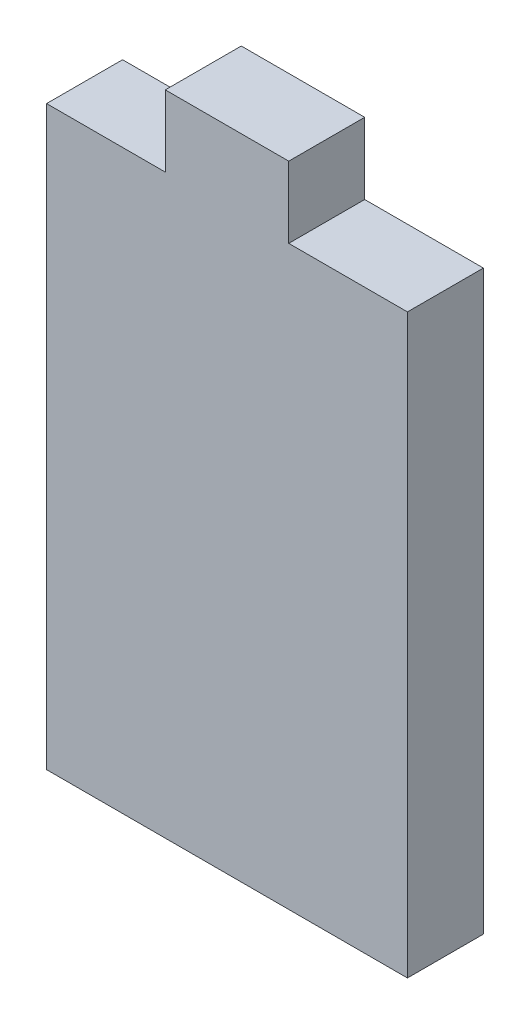
SolidWorks part; units mm, degrees
ref_plane "Front Plane" through (0, 0, 0) normal (0, 0, 1) x (1, 0, 0)
ref_plane "Top Plane" through (0, 0, 0) normal (0, 1, 0) x (1, 0, 0)
ref_plane "Right Plane" through (0, 0, 0) normal (1, 0, 0) x (0, 0, -1)
sketch "Sketch2" plane through (0, 0, 0) normal (0, 1, 0) x (1, 0, 0)
  line L1 (19.304, -4.064) -> (-19.304, -4.064)
  line L2 (19.304, -4.064) -> (19.304, 4.064)
  line L3 (19.304, 4.064) -> (-19.304, 4.064)
  line L4 (-19.304, -4.064) -> (-19.304, 4.064)
  line L5 (19.304, -4.064) -> (-19.304, 4.064) construction
  line L6 (19.304, 4.064) -> (-19.304, -4.064) construction
  point P0 (0, 0)
  dimension "D1" = 8.128
  dimension "D2" = 38.608
extrude "Boss-Extrude1" add sketch "Sketch2" along normal blind 61.722
sketch "Sketch3" plane through (0, 61.722, 0) normal (0, 1, 0) x (1, 0, 0)
  line L0 (19.304, 4.064) -> (-19.304, 4.064) construction
  line L1 (-6.604, 4.064) -> (6.604, 4.064)
  line L2 (-6.604, 4.064) -> (-6.604, -4.064)
  line L3 (-6.604, -4.064) -> (6.604, -4.064)
  line L4 (6.604, 4.064) -> (6.604, -4.064)
  line L5 (-19.304, -4.064) -> (19.304, -4.064) construction
  line L6 (19.304, -4.064) -> (19.304, 4.064) construction
  line L7 (-19.304, 4.064) -> (-19.304, -4.064) construction
  dimension "D1" = 12.7
  dimension "D2" = 12.7
extrude "Boss-Extrude2" add sketch "Sketch3" along normal blind 7.62
